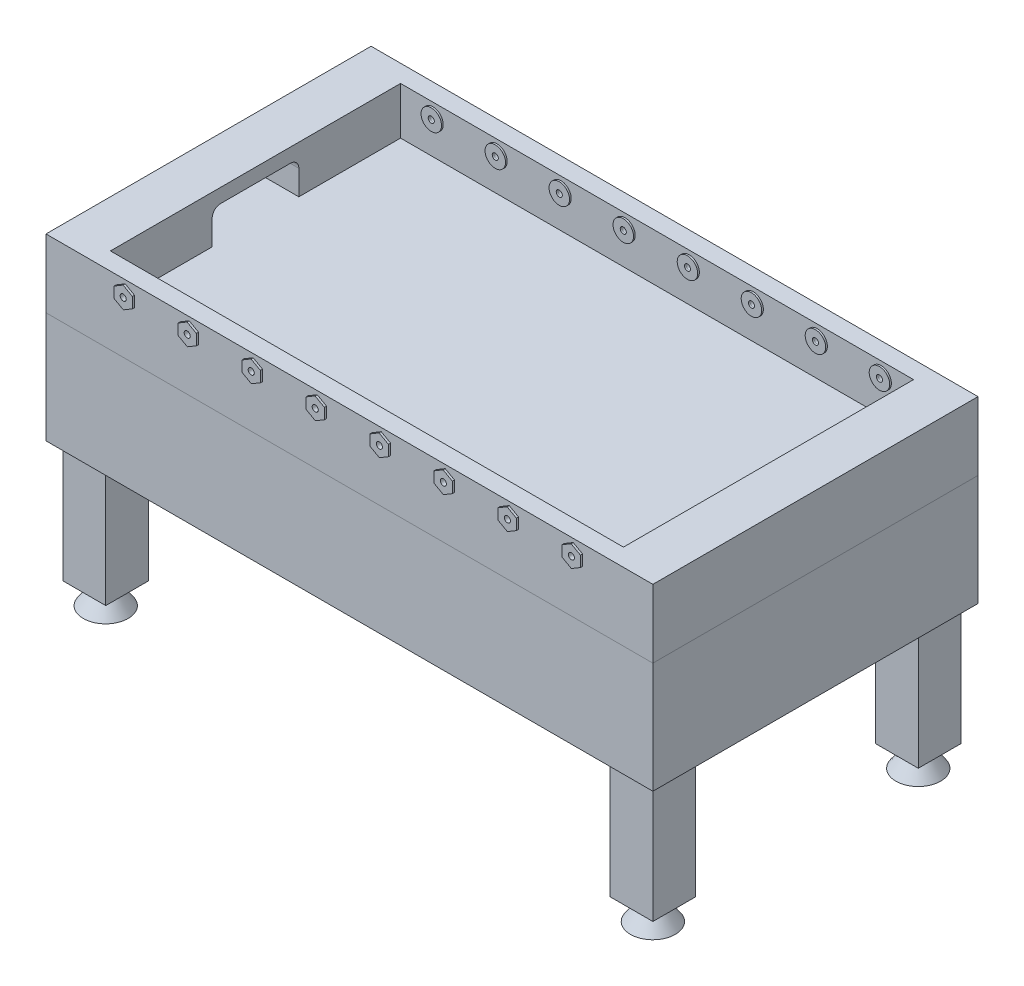
SolidWorks part; units mm, degrees
ref_plane "Front Plane" through (0, 0, 0) normal (0, 0, 1) x (1, 0, 0)
ref_plane "Top Plane" through (0, 0, 0) normal (0, 1, 0) x (1, 0, 0)
ref_plane "Right Plane" through (0, 0, 0) normal (1, 0, 0) x (0, 0, -1)
sketch "스케치1" plane through (0, 0, 0) normal (0, 1, 0) x (1, 0, 0)
  line L1 (711.2, -381) -> (-711.2, -381)
  line L2 (711.2, -381) -> (711.2, 381)
  line L3 (711.2, 381) -> (-711.2, 381)
  line L4 (-711.2, -381) -> (-711.2, 381)
  line L5 (711.2, -381) -> (-711.2, 381) construction
  line L6 (711.2, 381) -> (-711.2, -381) construction
  point P0 (0, 0)
  dimension "D1" = 1422.4
  dimension "D2" = 762
extrude "보스-돌출1" add sketch "스케치1" along normal blind 160
sketch "스케치2" plane through (0, 160, 0) normal (0, 1, 0) x (1, 0, 0)
  line L1 (601.2, -340) -> (-601.2, -340)
  line L2 (601.2, -340) -> (601.2, 340)
  line L3 (601.2, 340) -> (-601.2, 340)
  line L4 (-601.2, -340) -> (-601.2, 340)
  line L5 (601.2, -340) -> (-601.2, 340) construction
  line L6 (601.2, 340) -> (-601.2, -340) construction
  point P0 (0, 0)
  dimension "D1" = 1202.4
  dimension "D2" = 680
extrude "컷-돌출1" cut sketch "스케치2" against normal blind 111
sketch "스케치3" plane through (601.2, 0, 0) normal (-1, 0, 0) x (0, 0, 1)
  line L0 (340, 49) -> (-340, 49) construction
  line L2 (-101.6, 49) -> (-101.6, 127)
  line L3 (-101.6, 127) -> (101.6, 127)
  line L4 (101.6, 49) -> (101.6, 127)
  line L5 (0, 49) -> (101.6, 127) construction
  line L6 (-101.6, 127) -> (0, 49) construction
  line L7 (-148.063, 49) -> (174.1502, 49) construction
  line L8 (-101.6, 49) -> (101.6, 49)
  point P0 (0, 49)
  dimension "D1" = 203.2
extrude "컷-돌출2" cut sketch "스케치3" against normal blind 80
mirror "대칭 복사1" about plane through (0, 0, 0) normal (1, 0, 0) of "컷-돌출2"
sketch "스케치4" plane through (0, 0, -340) normal (0, 0, 1) x (1, 0, 0)
  line L0 (-601.2, 49) -> (601.2, 49) construction
  line L1 (-601.2, 160) -> (-601.2, 49) construction
  line L2 (601.2, 49) -> (601.2, 160) construction
  line L3 (0, -88) -> (0, 88) construction
  circle A0 centre (-525.2, 126.5) radius 24
  circle A1 centre (-375.2, 126.5) radius 24
  circle A2 centre (-225.2, 126.5) radius 24
  circle A3 centre (-75.2, 126.5) radius 24
  circle A4 centre (75.2, 126.5) radius 24
  circle A5 centre (225.2, 126.5) radius 24
  circle A6 centre (375.2, 126.5) radius 24
  circle A7 centre (525.2, 126.5) radius 24
  circle A8 centre (-525.2, 126.5) radius 7.1437
  circle A9 centre (-375.2, 126.5) radius 7.1438
  circle A10 centre (-225.2, 126.5) radius 7.1438
  circle A11 centre (-75.2, 126.5) radius 7.1437
  circle A12 centre (75.2, 126.5) radius 7.1437
  circle A13 centre (225.2, 126.5) radius 7.1438
  circle A14 centre (375.2, 126.5) radius 7.1438
  circle A15 centre (525.2, 126.5) radius 7.1437
  dimension "D3" = 48
  dimension "D4" = 48
  dimension "D6" = 150
  dimension "D8" = 14.2875
  dimension "D9" = 14.2875
  dimension "D10" = 14.2875
  dimension "D11" = 14.2875
  dimension "D1" = 76
  dimension "D2" = 77.5
  dimension "D5" = 150
  dimension "D7" = 150
extrude "보스-돌출2" add sketch "스케치4" along normal blind 4 separate body
mirror "대칭 복사2" about plane through (0, 0, 0) normal (0, 0, 1) of "보스-돌출2"
sketch "스케치5" plane through (0, 0, 0) normal (0, -1, 0) x (1, 0, 0)
  line L1 (711.2, -381) -> (-711.2, -381)
  line L2 (711.2, -381) -> (711.2, 381)
  line L3 (711.2, 381) -> (-711.2, 381)
  line L4 (-711.2, -381) -> (-711.2, 381)
  line L5 (711.2, -381) -> (-711.2, 381) construction
  line L6 (711.2, 381) -> (-711.2, -381) construction
  point P0 (0, 0)
extrude "보스-돌출3" add sketch "스케치5" along normal blind 260 separate body
sketch "스케치6" plane through (0, 0, -340) normal (0, 0, 1) x (1, 0, 0)
  circle A0 centre (-525.2, 126.5) radius 7.1438 construction
  circle A1 centre (-525.2, 126.5) radius 7.1437
  circle A2 centre (525.2, 126.5) radius 7.1438 construction
  circle A3 centre (375.2, 126.5) radius 7.1438 construction
  circle A4 centre (225.2, 126.5) radius 7.1438 construction
  circle A5 centre (-75.2, 126.5) radius 7.1438 construction
  circle A6 centre (-225.2, 126.5) radius 7.1438 construction
  circle A7 centre (-375.2, 126.5) radius 7.1438 construction
  circle A8 centre (525.2, 126.5) radius 7.1437
  circle A9 centre (375.2, 126.5) radius 7.1438
  circle A10 centre (225.2, 126.5) radius 7.1438
  circle A11 centre (-75.2, 126.5) radius 7.1437
  circle A12 centre (-225.2, 126.5) radius 7.1438
  circle A13 centre (-375.2, 126.5) radius 7.1438
  circle A14 centre (75.2, 126.5) radius 7.1438 construction
  circle A15 centre (75.2, 126.5) radius 7.1437
sketch "스케치7" plane through (0, -260, 0) normal (0, -1, 0) x (1, 0, 0)
  line L0 (711.2, 381) -> (-711.2, 381) construction
  line L1 (-691.2, 361) -> (-591.2, 361)
  line L2 (-691.2, 361) -> (-691.2, 261)
  line L3 (-691.2, 261) -> (-591.2, 261)
  line L4 (-591.2, 361) -> (-591.2, 261)
  line L5 (-691.2, 361) -> (-591.2, 261) construction
  line L6 (-691.2, 261) -> (-591.2, 361) construction
  line L7 (-711.2, 381) -> (-711.2, -381) construction
  line L8 (0, -414.92) -> (0, 414.92) construction
  line L9 (691.2, 261) -> (591.2, 261)
  line L10 (591.2, 361) -> (591.2, 261)
  line L11 (691.2, 361) -> (591.2, 361)
  line L12 (691.2, 361) -> (691.2, 261)
  line L13 (414.92, 0) -> (-414.92, 0) construction
  line L14 (691.2, -361) -> (691.2, -261)
  line L15 (691.2, -361) -> (591.2, -361)
  line L16 (591.2, -361) -> (591.2, -261)
  line L17 (691.2, -261) -> (591.2, -261)
  line L18 (-691.2, -261) -> (-591.2, -261)
  line L19 (-591.2, -361) -> (-591.2, -261)
  line L20 (-691.2, -361) -> (-591.2, -361)
  line L21 (-691.2, -361) -> (-691.2, -261)
  point P0 (-641.2, 311)
  point P5 (-663.9965, 331.0732)
  point P6 (-649.97, 322.8388)
  dimension "D1" = 100
  dimension "D2" = 100
  dimension "D3" = 70
  dimension "D4" = 70
extrude "보스-돌출4" add sketch "스케치7" along normal blind 284.4
sketch "스케치8" plane through (0, -544.4, 0) normal (0, -1, 0) x (1, 0, 0)
  line L2 (0, -414.92) -> (0, 414.92) construction
  line L3 (414.92, 0) -> (-414.92, 0) construction
  circle A4 centre (-641.2, 311) radius 17.5
  circle A5 centre (641.2, 311) radius 17.5
  circle A6 centre (641.2, -311) radius 17.5
  circle A7 centre (-641.2, -311) radius 17.5
  dimension "D1" = 35
extrude "보스-돌출5" add sketch "스케치8" along normal blind 50 draft 35 draft outward yes
sketch "스케치9" plane through (0, 0, 381) normal (0, 0, 1) x (1, 0, 0)
  line L0 (-353.3752, 114.3066) -> (-353.7278, 139.3042)
  line L1 (-503.3752, 114.3066) -> (-503.7278, 139.3042)
  line L2 (-503.7278, 139.3042) -> (-525.5526, 151.4975)
  line L3 (-525.5526, 151.4975) -> (-547.0248, 138.6934)
  line L4 (-547.0248, 138.6934) -> (-546.6722, 113.6958)
  line L5 (-546.6722, 113.6958) -> (-524.8474, 101.5025)
  line L6 (-524.8474, 101.5025) -> (-503.3752, 114.3066)
  line L7 (-353.7278, 139.3042) -> (-375.5526, 151.4975)
  line L8 (-375.5526, 151.4975) -> (-397.0248, 138.6934)
  line L9 (-397.0248, 138.6934) -> (-396.6722, 113.6958)
  line L10 (-396.6722, 113.6958) -> (-374.8474, 101.5025)
  line L11 (-374.8474, 101.5025) -> (-353.3752, 114.3066)
  line L12 (-203.3752, 114.3066) -> (-203.7278, 139.3042)
  line L13 (-203.7278, 139.3042) -> (-225.5526, 151.4975)
  line L14 (-225.5526, 151.4975) -> (-247.0248, 138.6934)
  line L15 (-247.0248, 138.6934) -> (-246.6722, 113.6958)
  line L16 (-246.6722, 113.6958) -> (-224.8474, 101.5025)
  line L17 (-224.8474, 101.5025) -> (-203.3752, 114.3066)
  line L18 (-53.3752, 114.3066) -> (-53.7278, 139.3042)
  line L19 (-53.7278, 139.3042) -> (-75.5526, 151.4975)
  line L20 (-75.5526, 151.4975) -> (-97.0248, 138.6934)
  line L21 (-97.0248, 138.6934) -> (-96.6722, 113.6958)
  line L22 (-96.6722, 113.6958) -> (-74.8474, 101.5025)
  line L23 (-74.8474, 101.5025) -> (-53.3752, 114.3066)
  line L24 (96.6248, 114.3066) -> (96.2722, 139.3042)
  line L25 (96.2722, 139.3042) -> (74.4474, 151.4975)
  line L26 (74.4474, 151.4975) -> (52.9752, 138.6934)
  line L27 (52.9752, 138.6934) -> (53.3278, 113.6958)
  line L28 (53.3278, 113.6958) -> (75.1526, 101.5025)
  line L29 (75.1526, 101.5025) -> (96.6248, 114.3066)
  line L30 (246.6248, 114.3066) -> (246.2722, 139.3042)
  line L31 (246.2722, 139.3042) -> (224.4474, 151.4975)
  line L32 (224.4474, 151.4975) -> (202.9752, 138.6934)
  line L33 (202.9752, 138.6934) -> (203.3278, 113.6958)
  line L34 (203.3278, 113.6958) -> (225.1526, 101.5025)
  line L35 (225.1526, 101.5025) -> (246.6248, 114.3066)
  line L36 (396.6248, 114.3066) -> (396.2722, 139.3042)
  line L37 (396.2722, 139.3042) -> (374.4474, 151.4975)
  line L38 (374.4474, 151.4975) -> (352.9752, 138.6934)
  line L39 (352.9752, 138.6934) -> (353.3278, 113.6958)
  line L40 (353.3278, 113.6958) -> (375.1526, 101.5025)
  line L41 (375.1526, 101.5025) -> (396.6248, 114.3066)
  line L42 (546.6248, 114.3066) -> (546.2722, 139.3042)
  line L43 (546.2722, 139.3042) -> (524.4474, 151.4975)
  line L44 (524.4474, 151.4975) -> (502.9752, 138.6934)
  line L45 (502.9752, 138.6934) -> (503.3278, 113.6958)
  line L46 (503.3278, 113.6958) -> (525.1526, 101.5025)
  line L47 (525.1526, 101.5025) -> (546.6248, 114.3066)
  circle A0 centre (-525.2, 126.5) radius 21.6506 construction
  circle A1 centre (-375.2, 126.5) radius 21.6506 construction
  circle A2 centre (-225.2, 126.5) radius 21.6506 construction
  circle A3 centre (-75.2, 126.5) radius 21.6506 construction
  circle A4 centre (74.8, 126.5) radius 21.6506 construction
  circle A5 centre (224.8, 126.5) radius 21.6506 construction
  circle A6 centre (374.8, 126.5) radius 21.6506 construction
  circle A7 centre (524.8, 126.5) radius 21.6506 construction
  dimension "D1" = 25
  dimension "D2" = 8
extrude "보스-돌출6" add sketch "스케치9" along normal blind 5
mirror "대칭 복사3" about plane through (0, 0, 0) normal (0, 0, 1) of "보스-돌출6"
sketch "스케치10" plane through (0, 0, -340) normal (0, 0, 1) x (1, 0, 0)
  circle A0 centre (525.2, 126.5) radius 7.1438 construction
  circle A1 centre (375.2, 126.5) radius 7.1438 construction
  circle A2 centre (225.2, 126.5) radius 7.1438 construction
  circle A3 centre (75.2, 126.5) radius 7.1438 construction
  circle A4 centre (-75.2, 126.5) radius 7.1438 construction
  circle A5 centre (-225.2, 126.5) radius 7.1438 construction
  circle A6 centre (-375.2, 126.5) radius 7.1438 construction
  circle A7 centre (-525.2, 126.5) radius 7.1438 construction
  circle A8 centre (525.2, 126.5) radius 7.1437
  circle A9 centre (375.2, 126.5) radius 7.1438
  circle A10 centre (225.2, 126.5) radius 7.1438
  circle A11 centre (75.2, 126.5) radius 7.1437
  circle A12 centre (-75.2, 126.5) radius 7.1437
  circle A13 centre (-225.2, 126.5) radius 7.1438
  circle A14 centre (-375.2, 126.5) radius 7.1438
  circle A15 centre (-525.2, 126.5) radius 7.1437
extrude "컷-돌출4" cut sketch "스케치10" against normal through all both and the other way through all
sketch "스케치11" plane through (0, 0, -381) normal (0, 0, -1) x (-1, 0, 0)
  line L0 (-81, 0) -> (81, 0)
  line L2 (-81, 0) -> (-81, -85)
  line L3 (-81, -85) -> (81, -85)
  line L4 (81, 0) -> (81, -85)
  line L5 (0, 0) -> (81, -85) construction
  line L6 (-81, -85) -> (0, 0) construction
  point P0 (0, 0)
  dimension "D1" = 162
  dimension "D2" = 85
extrude "컷-돌출5" cut sketch "스케치11" against normal up to surface (381 mm away) and the other way through all up to plane "Front Plane"
sketch "스케치14" plane through (-81, 0, 0) normal (1, 0, 0) x (0, 0, -1)
  line L0 (0, -85) -> (361, -108.114)
  line L3 (361, -85) -> (0, -85)
  line L4 (381, 0) -> (0, 0)
  line L5 (0, 0) -> (0, -85)
  line L6 (0, -85) -> (381, -85)
  line L7 (381, -85) -> (381, 0)
  line L8 (381, 0) -> (0, 0) construction
  line L9 (0, 0) -> (0, -85) construction
  line L10 (0, -85) -> (361, -85) construction
  line L11 (381, -85) -> (381, 0) construction
  line L12 (361, -85) -> (361, -108.114)
  dimension "D2" = 23.114
  dimension "D3" = 20
  dimension "D1" = 0
extrude "컷-돌출6" cut sketch "스케치14" along normal up to surface (162 mm away) up to face at (81, -42.5, -190.5)
sketch "스케치15" plane through (81, 0, 0) normal (-1, 0, 0) x (0, 0, 1)
  line L0 (-361, 0) -> (-361, -108.114)
  line L3 (-361, 0) -> (0, 0)
  line L4 (0, -85) -> (0, 0)
  line L5 (-361, -108.114) -> (0, -85)
  line L6 (-381, -85) -> (-361, -85)
  line L7 (-361, -85) -> (-361, -108.114)
  line L8 (-361, -108.114) -> (0, -85)
  line L9 (0, -85) -> (0, 0)
  line L10 (0, 0) -> (-381, 0)
  line L11 (-381, 0) -> (-381, -85)
  line L12 (-381, -85) -> (-361, -85) construction
  line L13 (-361, -85) -> (-361, -108.114) construction
  line L14 (-361, -108.114) -> (0, -85) construction
  line L15 (0, -85) -> (0, 0) construction
  line L16 (0, 0) -> (-381, 0) construction
  line L17 (-381, 0) -> (-381, -85) construction
  dimension "D1" = 0
extrude "컷-돌출7" cut sketch "스케치15" against normal blind 10
mirror "대칭 복사4" about plane through (0, 0, 0) normal (1, 0, 0) of "컷-돌출7"
fillet "필렛1" radius 20 4 edges at (-641.2, 127, 101.6) (-641.2, 127, -101.6) (641.2, 127, 101.6) (641.2, 127, -101.6)
